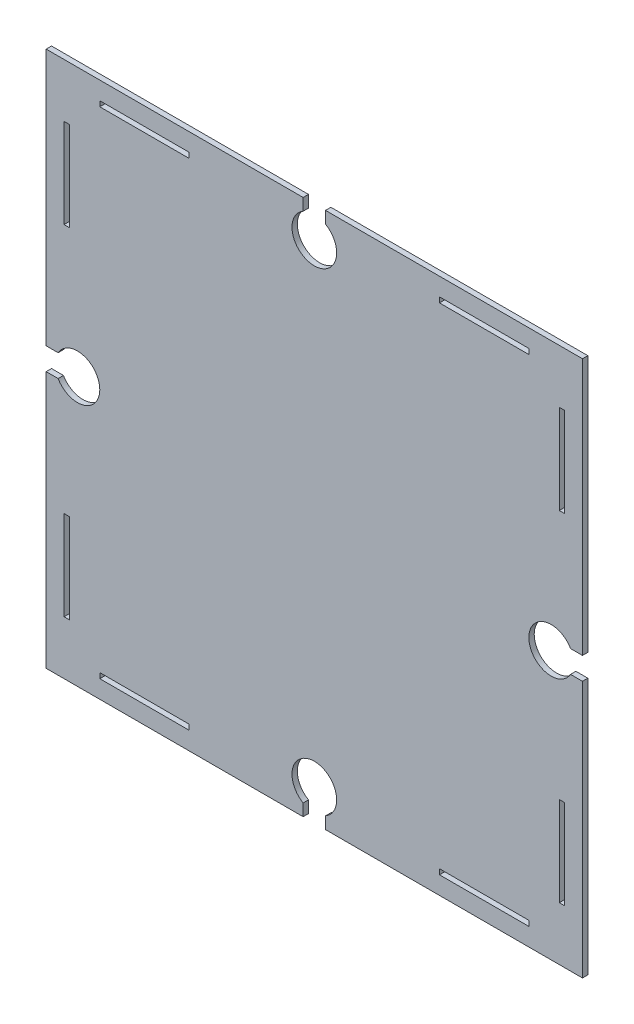
SolidWorks part; units mm, degrees
ref_plane "Plan de face" through (0, 0, 0) normal (0, 0, 1) x (1, 0, 0)
ref_plane "Plan de dessus" through (0, 0, 0) normal (0, 1, 0) x (1, 0, 0)
ref_plane "Plan de droite" through (0, 0, 0) normal (1, 0, 0) x (0, 0, -1)
sketch "Esquisse2" plane through (0, 0, 0) normal (0, 0, 1) x (1, 0, 0)
  line L1 (150, -150) -> (-150, -150)
  line L2 (150, -150) -> (150, 150)
  line L3 (150, 150) -> (-150, 150)
  line L4 (-150, -150) -> (-150, 150)
  line L5 (150, -150) -> (-150, 150) construction
  line L6 (150, 150) -> (-150, -150) construction
  point P0 (0, 0)
  dimension "D1" = 300
  dimension "D2" = 300
extrude "Boss.-Extru.1" add sketch "Esquisse2" along normal blind 3
sketch "Esquisse3" plane through (0, 0, 3) normal (0, 0, 1) x (1, 0, 0)
  line L0 (-120, 140) -> (-70, 140)
  line L1 (-70, 140) -> (-70, 137.05)
  line L2 (-70, 137.05) -> (-120, 137.05)
  line L3 (-120, 137.05) -> (-120, 140)
  line L4 (-150, 150) -> (-150, -150) construction
  line L5 (-140, 120) -> (-137.05, 120)
  line L6 (-140, 120) -> (-140, 70)
  line L7 (-140, 70) -> (-137.05, 70)
  line L8 (-137.05, 120) -> (-137.05, 70)
  line L9 (150, 150) -> (-150, 150) construction
  dimension "D1" = 2.95
  dimension "D2" = 50
  dimension "D3" = 2.95
  dimension "D4" = 50
  dimension "D5" = 10
  dimension "D6" = 30
  dimension "D7" = 30
  dimension "D8" = 10
extrude "Enlèv. mat.-Extru.2" cut sketch "Esquisse3" against normal blind 6
sketch "Esquisse5" plane through (0, 0, 0) normal (0, 0, -1) x (-1, 0, 0)
  line L0 (150, 150) -> (150, -150) construction
  line L1 (137.05, -120) -> (140, -120)
  line L2 (137.05, -120) -> (137.05, -70)
  line L3 (137.05, -70) -> (140, -70)
  line L4 (140, -120) -> (140, -70)
  line L5 (120, -140) -> (70, -140)
  line L6 (120, -140) -> (120, -137.05)
  line L7 (120, -137.05) -> (70, -137.05)
  line L8 (70, -140) -> (70, -137.05)
  line L9 (150, -150) -> (-150, -150) construction
  line L10 (-150, -150) -> (-150, 150) construction
  line L11 (-70, -140) -> (-120, -140)
  line L12 (-70, -140) -> (-70, -137.05)
  line L13 (-70, -137.05) -> (-120, -137.05)
  line L14 (-120, -140) -> (-120, -137.05)
  line L15 (-137.05, -120) -> (-140, -120)
  line L16 (-137.05, -120) -> (-137.05, -70)
  line L17 (-137.05, -70) -> (-140, -70)
  line L18 (-140, -120) -> (-140, -70)
  line L19 (-150, 150) -> (150, 150) construction
  line L20 (-137.05, 70) -> (-140, 70)
  line L21 (-137.05, 70) -> (-137.05, 120)
  line L22 (-137.05, 120) -> (-140, 120)
  line L23 (-140, 70) -> (-140, 120)
  line L24 (-70, 137.05) -> (-120, 137.05)
  line L25 (-70, 137.05) -> (-70, 140)
  line L26 (-70, 140) -> (-120, 140)
  line L27 (-120, 137.05) -> (-120, 140)
  point P12 (138.525, -120)
  dimension "D1" = 50
  dimension "D2" = 50
  dimension "D3" = 2.95
  dimension "D4" = 2.95
  dimension "D5" = 30
  dimension "D6" = 10
  dimension "D7" = 10
  dimension "D8" = 30
  dimension "D9" = 10
  dimension "D10" = 10
  dimension "D11" = 30
  dimension "D12" = 30
  dimension "D13" = 2.95
  dimension "D14" = 50
  dimension "D15" = 50
  dimension "D16" = 2.95
  dimension "D17" = 10
  dimension "D18" = 2.95
  dimension "D19" = 50
  dimension "D20" = 30
  dimension "D21" = 50
  dimension "D22" = 30
  dimension "D23" = 10
  dimension "D24" = 2.95
extrude "Enlèv. mat.-Extru.3" cut sketch "Esquisse5" against normal blind 6
sketch "Esquisse6" plane through (0, 0, 0) normal (0, 0, -1) x (-1, 0, 0)
  line L0 (0, -150) -> (0, 150) construction
  line L1 (150, -150) -> (-150, -150) construction
  line L2 (-150, 150) -> (150, 150) construction
  line L3 (150, 0) -> (-150, 0) construction
  line L4 (150, 150) -> (150, -150) construction
  line L5 (-150, -150) -> (-150, 150) construction
  line L6 (132.5, -12.5) -> (132.5, 0) construction
  line L7 (132.5, 0) -> (132.5, 12.5) construction
  line L8 (132.5, -6.25) -> (150, -6.25)
  line L9 (132.5, 6.25) -> (150, 6.25)
  line L10 (150, 6.25) -> (150, -6.25)
  line L11 (0, -132.5) -> (12.5, -132.5) construction
  line L12 (0, -132.5) -> (-12.5, -132.5) construction
  line L13 (6.25, -150) -> (6.25, -143.3253)
  line L14 (-6.25, -150) -> (-6.25, -143.3253)
  line L15 (6.25, -150) -> (-6.25, -150)
  line L17 (150, 0) -> (120, 0) construction
  circle A0 centre (132.5, 0) radius 12.5
  arc A1 (-6.25, -143.3253) -> (6.25, -143.3253) centre (0, -132.5) cw
  point P22 (0, -120)
  dimension "D1" = 25
  dimension "D2" = 12.5
  dimension "D4" = 30
  dimension "D5" = 25
  dimension "D6" = 30
  dimension "D3" = 12.5
extrude "Enlèv. mat.-Extru.4" cut sketch "Esquisse6" against normal blind 6
mirror "Symétrie1" about plane through (0, 0, 0) normal (1, 0, 0) of "Enlèv. mat.-Extru.4"
mirror "Symétrie2" about plane through (0, 0, 0) normal (0, 1, 0) of "Symétrie1"
